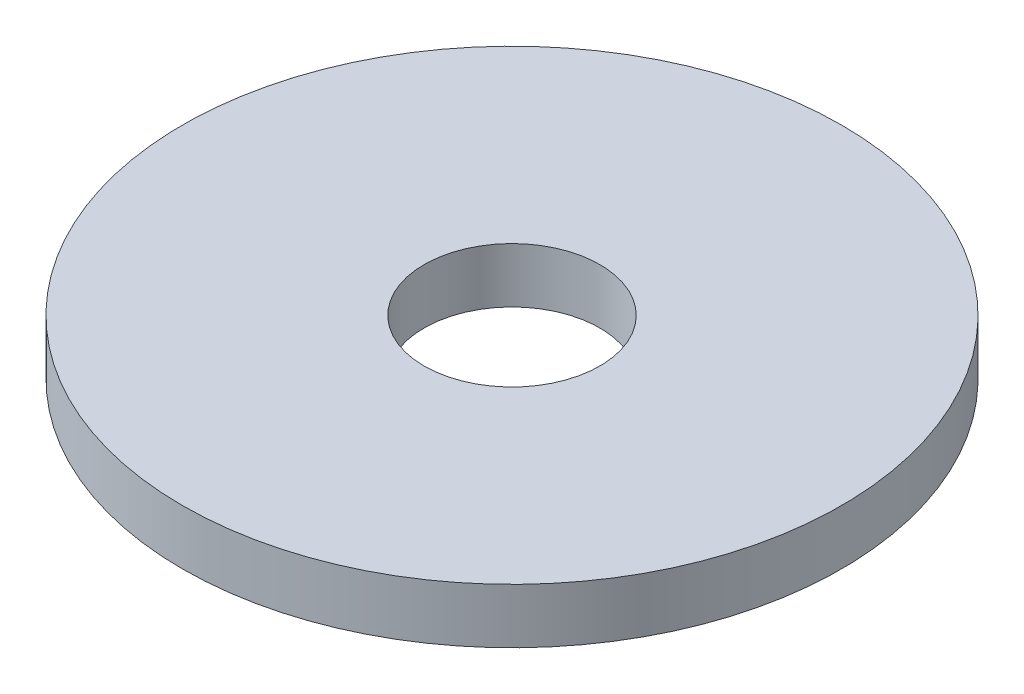
SolidWorks part; units mm, degrees
material "AISI 304"
ref_plane "前视基准面" through (0, 0, 0) normal (0, 0, 1) x (1, 0, 0)
ref_plane "上视基准面" through (0, 0, 0) normal (0, 1, 0) x (1, 0, 0)
ref_plane "右视基准面" through (0, 0, 0) normal (1, 0, 0) x (0, 0, -1)
sketch "草图1" plane through (0, 0, 0) normal (0, 1, 0) x (1, 0, 0)
  circle A0 centre (0, 0) radius 1.6
  circle A1 centre (0, 0) radius 6
  dimension "D1" = 3.2
  dimension "D2" = 12
extrude "凸台-拉伸1" add sketch "草图1" along normal blind 1
